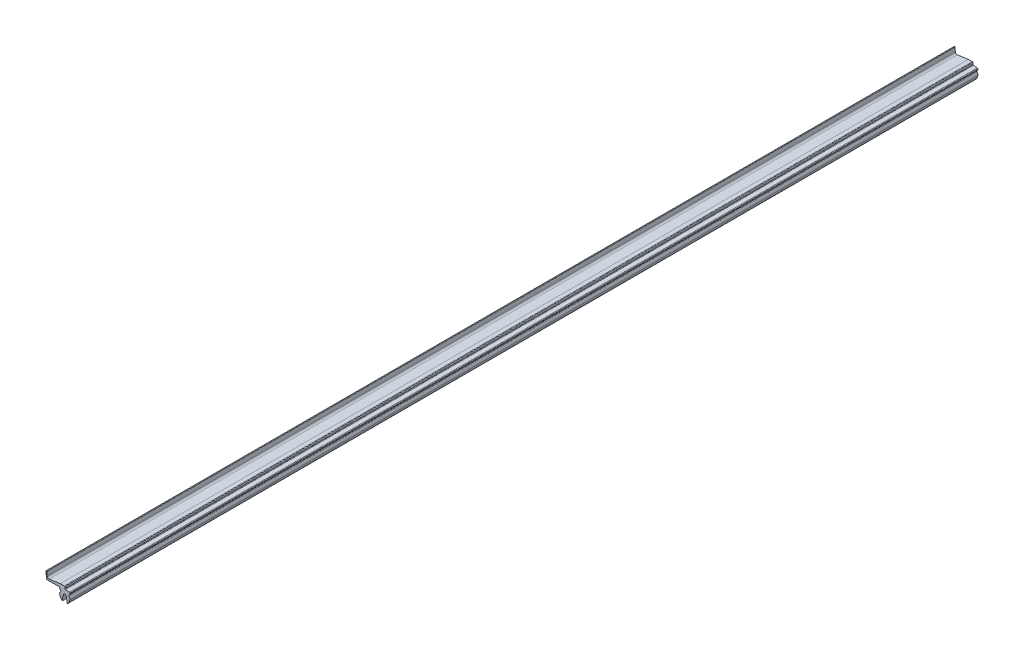
SolidWorks part; units mm, degrees
material "Santoprene"
ref_plane "Front" through (0, 0, 0) normal (0, 0, 1) x (1, 0, 0)
ref_plane "Top" through (0, 0, 0) normal (0, 1, 0) x (1, 0, 0)
ref_plane "Right" through (0, 0, 0) normal (1, 0, 0) x (0, 0, -1)
sketch "Sk Main Extrusion" plane through (0, 0, 0) normal (0, 0, 1) x (1, 0, 0)
  line L0 (-19.5648, 0) -> (-5.7096, 0)
  line L5 (5.0177, 0.3867) -> (0.6734, 0.7365)
  line L6 (-0.7477, 3.5221) -> (-4.9287, 3.5221)
  line L7 (-4.9287, 3.5221) -> (-17.0634, 1.8669)
  line L8 (-19.2669, 3.6241) -> (-19.6423, 7.8364)
  line L9 (-20.6388, 7.7527) -> (-20.0633, 0.4607)
  arc A0 (-20.0633, 0.4607) -> (-19.5648, 0) centre (-19.5648, 0.5) ccw
  arc A1 (-5.7096, 0) -> (-4.6433, -2.5779) centre (-1.7993, 0.1079) ccw
  arc A2 (-4.7435, -4.0356) -> (-4.6433, -2.5779) centre (-5.3746, -3.2599) ccw
  arc A3 (-4.7435, -4.0356) -> (-5.6248, -6.593) centre (-3.1264, -6.0234) ccw
  arc A4 (-5.6248, -6.593) -> (-3.4312, -11.153) centre (5.4705, -4.0634) ccw
  arc A5 (-3.4312, -11.153) -> (-2.5069, -11.5944) centre (-2.5153, -10.4235) ccw
  arc A6 (-1.5838, -5.1989) -> (-2.5069, -11.5944) centre (18.6308, -11.381) ccw
  arc A7 (1.5838, -5.1989) -> (-1.5838, -5.1989) centre (0, -5.6832) ccw
  arc A8 (2.5069, -11.5944) -> (1.5838, -5.1989) centre (-18.6308, -11.381) ccw
  arc A9 (2.5069, -11.5944) -> (3.4312, -11.153) centre (2.5153, -10.4235) ccw
  arc A10 (3.4312, -11.153) -> (5.6248, -6.593) centre (-5.4705, -4.0634) ccw
  arc A11 (5.6248, -6.593) -> (4.7435, -4.0356) centre (3.1264, -6.0234) ccw
  arc A12 (4.6433, -2.5779) -> (4.7435, -4.0356) centre (5.3746, -3.2599) ccw
  arc A13 (4.6433, -2.5779) -> (5.6737, -0.4311) centre (1.7993, 0.1079) ccw
  arc A14 (5.6737, -0.4311) -> (5.0177, 0.3867) centre (4.9598, -0.3318) ccw
  arc A15 (0.2186, 1.5444) -> (0.6734, 0.7365) centre (0.7183, 1.2938) ccw
  arc A16 (0.2186, 1.5444) -> (0, 3.1876) centre (-1.0991, 2.2053) ccw
  arc A17 (0, 3.1876) -> (-0.7477, 3.5221) centre (-0.7477, 2.5193) ccw
  arc A18 (-19.2669, 3.6241) -> (-17.0634, 1.8669) centre (-17.3267, 3.797) ccw
  arc A19 (-19.6423, 7.8364) -> (-20.6388, 7.7527) centre (-20.1403, 7.7921) ccw
  point P0 (0, 0)
extrude "Main Extrusion" add sketch "Sk Main Extrusion" against normal blind 1000
equation "\"Weight kg\"= round ( \"SW-Mass\" , 2 )"
equation "\"Weight lbs\"= round ( \"SW-Mass\" * 2.2046 , 2 )"
equation "\"Length mm\"= round ( \"Length@Main Extrusion\" , 2 )"
equation "\"Length in\"= round ( \"Length@Main Extrusion\" / 25.4 , 3 )"
